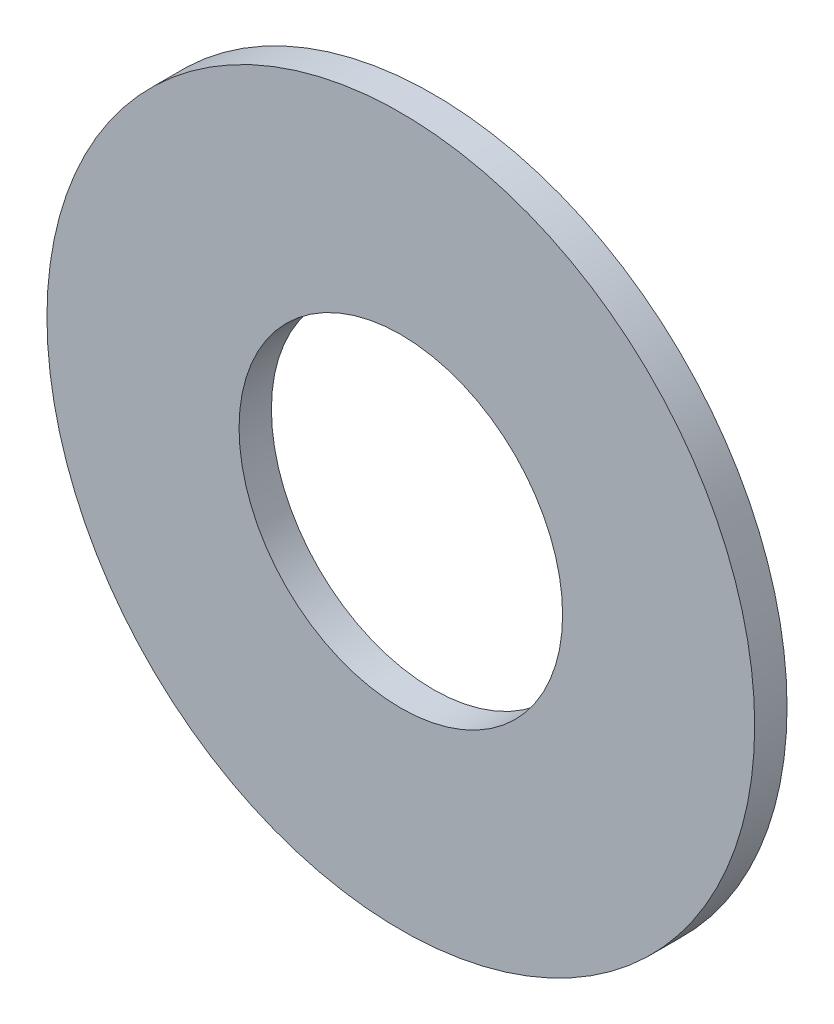
SolidWorks part; units mm, degrees
ref_plane "Front Plane" through (0, 0, 0) normal (0, 0, 1) x (1, 0, 0)
ref_plane "Top Plane" through (0, 0, 0) normal (0, 1, 0) x (1, 0, 0)
ref_plane "Right Plane" through (0, 0, 0) normal (1, 0, 0) x (0, 0, -1)
sketch "Sketch1" plane through (0, 0, 0) normal (0, 0, 1) x (1, 0, 0)
  circle A0 centre (0, 0) radius 2.54
  circle A1 centre (0, 0) radius 5.5562
  dimension "ID" = 5.08
  dimension "OD" = 11.1125
extrude "Extrude1" add sketch "Sketch1" against normal blind 0.508
